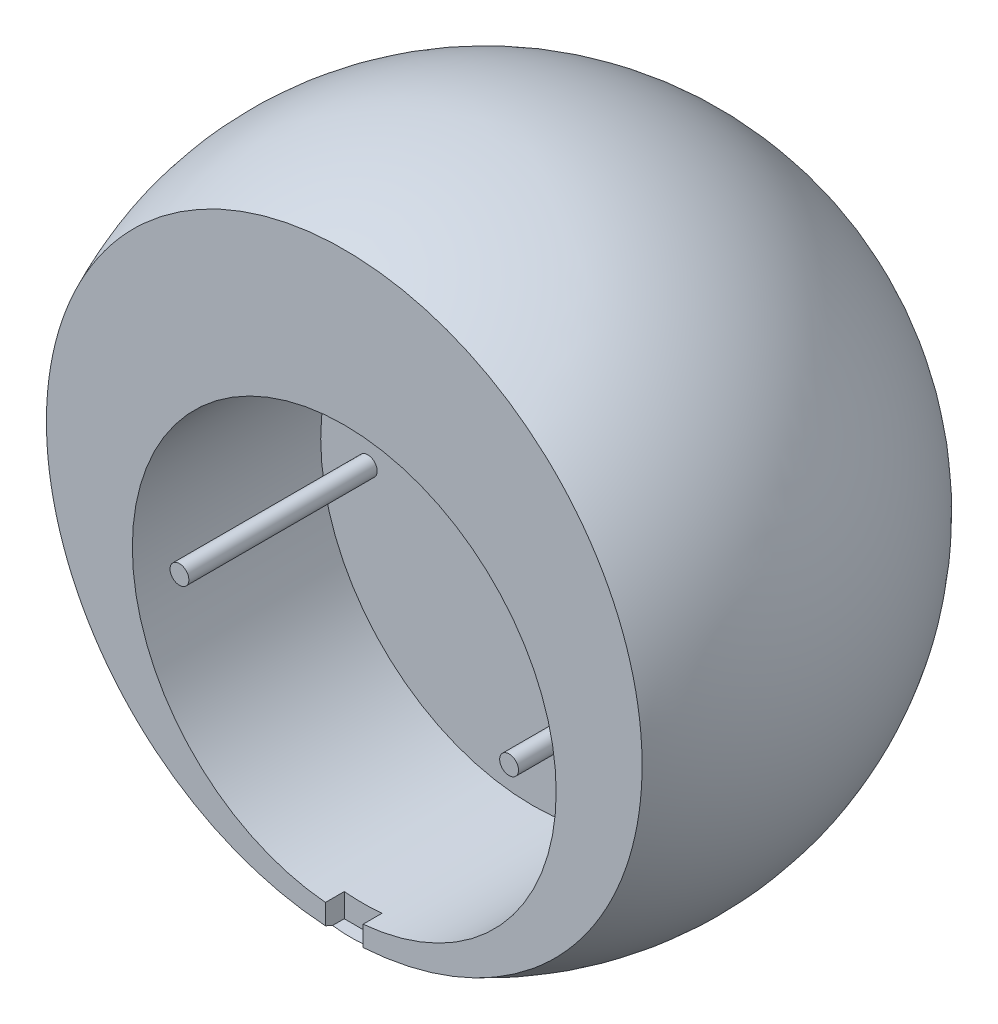
SolidWorks part; units mm, degrees
ref_plane "Front Plane" through (0, 0, 0) normal (0, 0, 1) x (1, 0, 0)
ref_plane "Top Plane" through (0, 0, 0) normal (0, 1, 0) x (1, 0, 0)
ref_plane "Right Plane" through (0, 0, 0) normal (1, 0, 0) x (0, 0, -1)
sketch "Sketch2" plane through (0, 0, 0) normal (0, 0, 1) x (1, 0, 0)
  line L0 (0, 0) -> (70, 0)
  arc A0 (0, 0) -> (70, 0) centre (35, 0) cw
  dimension "D1" = 70
revolve "Revolve1" add sketch "Sketch2" angle 360 about L0
ref_plane "Plane1" through (0, 0, 35) normal (0, 0, 1) x (1, 0, 0)
ref_plane "Plane2" through (0, 0, -5) normal (0, 0, 1) x (1, 0, 0)
sketch "Sketch6" plane through (0, 0, -5) normal (0, 0, 1) x (1, 0, 0)
  line L0 (17.5, -7) -> (52.5, -7) construction
  circle A0 centre (35, -7) radius 22.5
  circle A1 centre (17.5, -7) radius 1
  circle A2 centre (52.5, -7) radius 1
  dimension "D1" = 45
extrude "Cut-Extrude8" cut sketch "Sketch6" along normal blind 20
sketch "Sketch7" plane through (0, 0, 35) normal (0, 0, 1) x (1, 0, 0)
  line L0 (0, 0) -> (70, 0) construction
  circle A0 centre (35, 0) radius 35 construction
  circle A1 centre (35, 0) radius 7.9
  dimension "D1" = 15.8
extrude "Cut-Extrude9" cut sketch "Sketch7" against normal blind 20
sketch "Sketch8" plane through (0, 0, 35) normal (0, 0, 1) x (1, 0, 0)
  line L1 (-2.0998, 36.2866) -> (72.5063, 36.2866)
  line L2 (-2.0998, 36.2866) -> (-2.0998, -36.5915)
  line L3 (-2.0998, -36.5915) -> (72.5063, -36.5915)
  line L4 (72.5063, 36.2866) -> (72.5063, -36.5915)
extrude "Cut-Extrude10" cut sketch "Sketch8" against normal blind 20
ref_plane "Plane3" through (0, 0, 15) normal (0, 0, 1) x (1, 0, 0)
sketch "Sketch10" plane through (0, 0, 15) normal (0, 0, 1) x (1, 0, 0)
  line L0 (33, -29.4109) -> (37, -29.4109)
  line L4 (37, -29.4109) -> (37, -31.9109)
  line L5 (37, -31.9109) -> (33, -31.9109)
  line L6 (33, -31.9109) -> (33, -29.4109)
  circle A0 centre (35, -7) radius 22.5 construction
  circle A1 centre (35, -7) radius 22.5 construction
  dimension "D1" = 4
  dimension "D2" = 2.5
extrude "Cut-Extrude11" cut sketch "Sketch10" against normal blind 2
